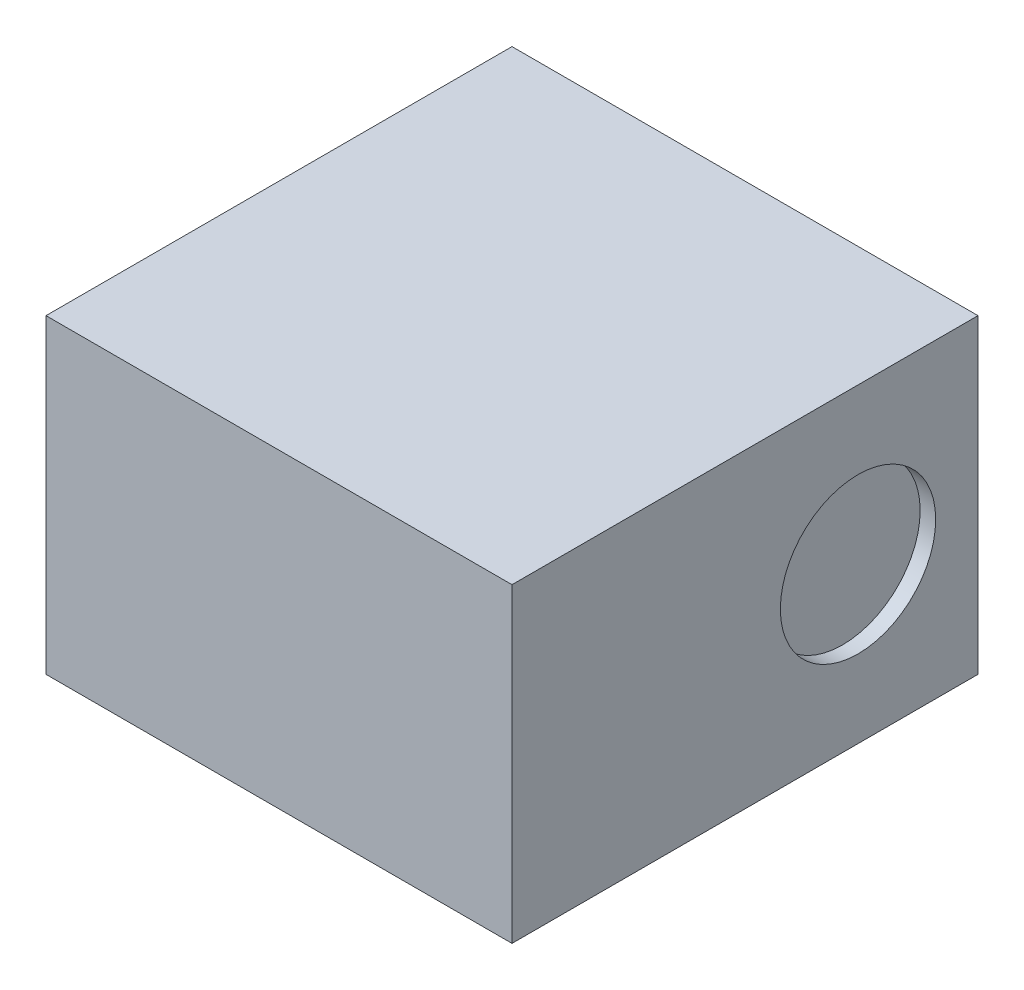
SolidWorks part; units mm, degrees
ref_plane "Front Plane" through (0, 0, 0) normal (0, 0, 1) x (1, 0, 0)
ref_plane "Top Plane" through (0, 0, 0) normal (0, 1, 0) x (1, 0, 0)
ref_plane "Right Plane" through (0, 0, 0) normal (1, 0, 0) x (0, 0, -1)
sketch "Sketch1" plane through (0, 0, 0) normal (0, 1, 0) x (1, 0, 0)
  line L0 (0, 0) -> (18.6879, 0) construction
  line L1 (0, 0) -> (0, -14.4281) construction
  line L3 (-0.75, 0.75) -> (0.75, 0.75)
  line L4 (-0.75, 0.75) -> (-0.75, -0.75)
  line L5 (-0.75, -0.75) -> (0.75, -0.75)
  line L6 (0.75, 0.75) -> (0.75, -0.75)
  dimension "D1" = 1.5
extrude "Boss-Extrude1" add sketch "Sketch1" along normal blind 1
sketch "Sketch2" plane through (0.75, 0, 0) normal (1, 0, 0) x (0, 0, -1)
  line L0 (-0.75, 0.5) -> (0.75, 0.5) construction
  line L1 (-0.75, 1) -> (-0.75, 0) construction
  line L2 (0.75, 1) -> (0.75, 0) construction
  circle A1 centre (0.3638, 0.5) radius 0.25
  dimension "D1" = 0.5
extrude "Cut-Extrude1" cut sketch "Sketch2" against normal blind 0.05
